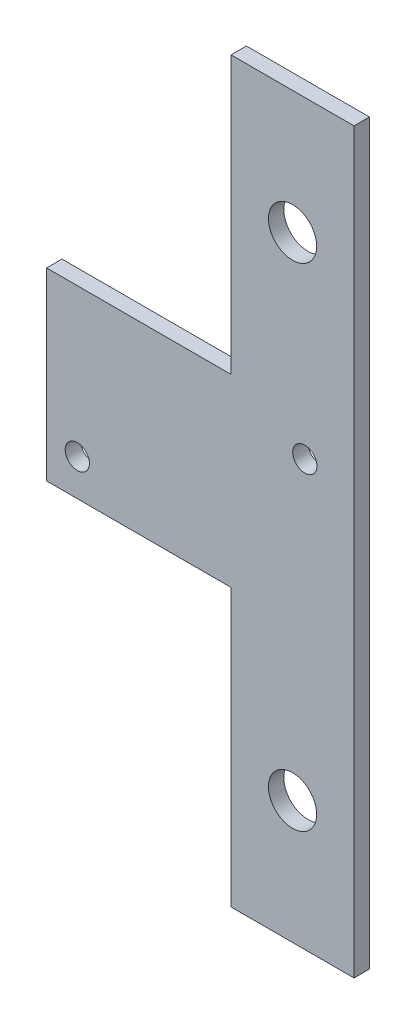
SolidWorks part; units mm, degrees
material "6061-T6 (SS)"
ref_plane "Front Plane" through (0, 0, 0) normal (0, 0, 1) x (1, 0, 0)
ref_plane "Top Plane" through (0, 0, 0) normal (0, 1, 0) x (1, 0, 0)
ref_plane "Right Plane" through (0, 0, 0) normal (1, 0, 0) x (0, 0, -1)
sketch "Sketch1" plane through (0, 0, 0) normal (0, 0, 1) x (1, 0, 0)
  line L0 (-12.3843, 970.3945) -> (-25.0843, 970.3945)
  line L1 (-40.9593, 1002.7363) -> (-17.4674, 1014.2528) construction
  line L2 (-17.4674, 1014.2528) -> (-17.4674, 1002.7363) construction
  line L3 (-25.0843, 970.3945) -> (-25.0843, 998.9695)
  line L4 (-25.0843, 998.9695) -> (-44.1343, 998.9695)
  line L5 (-44.1343, 998.9695) -> (-44.1343, 1018.0195)
  line L6 (-44.1343, 1018.0195) -> (-25.0843, 1018.0195)
  line L7 (-25.0843, 1018.0195) -> (-25.0843, 1046.5945)
  line L8 (-25.0843, 1046.5945) -> (-12.3843, 1046.5945)
  line L9 (-12.3843, 1046.5945) -> (-12.3843, 970.3945)
  line L10 (-18.7343, 970.3945) -> (-18.7343, 1046.5945) construction
  line L11 (-18.7343, 1008.4945) -> (-44.1343, 1008.4945) construction
  line L12 (-17.4674, 1002.7363) -> (-40.9593, 1002.7363) construction
  line L13 (-40.9593, 1002.7363) -> (-40.9593, 1014.2528) construction
  line L14 (-40.9593, 1014.2528) -> (-17.4674, 1014.2528) construction
  circle A0 centre (-18.7343, 983.0945) radius 2.4892
  circle A1 centre (-18.7343, 1033.8945) radius 2.4892
  circle A2 centre (-40.9593, 1002.7363) radius 1.25 construction
  circle A4 centre (-40.9593, 1002.7363) radius 1.25
  circle A5 centre (-17.4674, 1014.2528) radius 1.25
  point P20 (-29.2134, 1008.4945)
  dimension "D2" = 12.7
  dimension "D3" = 12.7
  dimension "D5" = 4.9784
  dimension "D10" = 3.175
  dimension "D1" = 12.7
  dimension "D4" = 76.2
  dimension "D6" = 19.05
  dimension "D7" = 19.05
  dimension "D8" = 23.4919
  dimension "D9" = 26.163
extrude "Boss-Extrude1" add sketch "Sketch1" along normal blind 1.5875
equation "\"Thick\"= \"in\""
